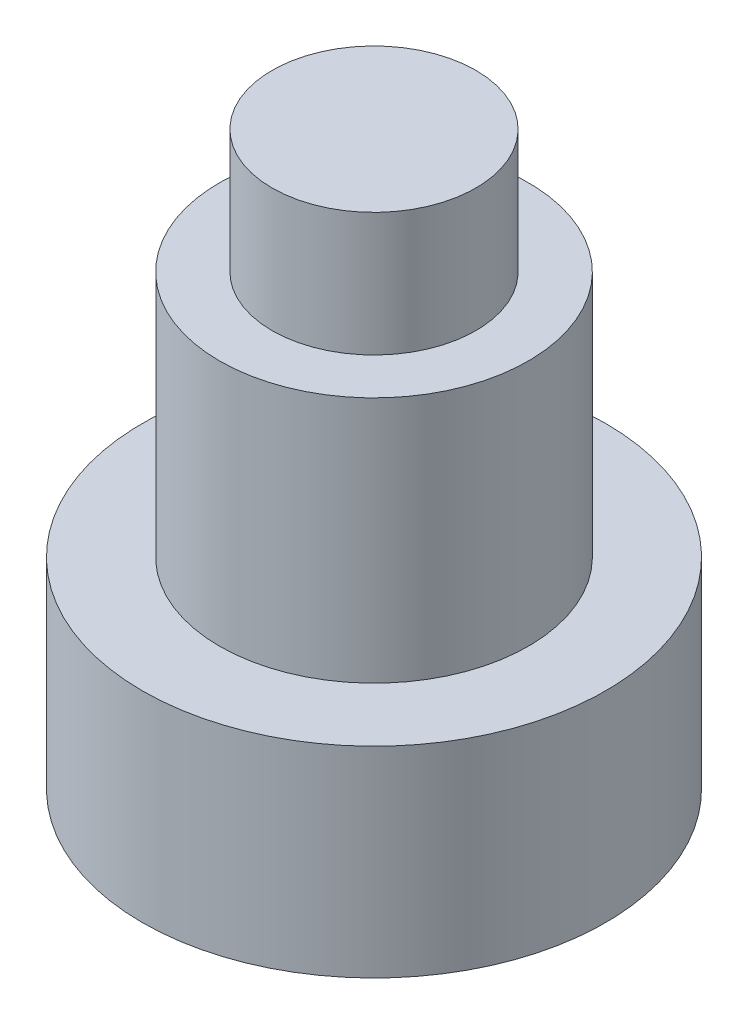
SolidWorks part; units mm, degrees
ref_plane "Front Plane" through (0, 0, 0) normal (0, 0, 1) x (1, 0, 0)
ref_plane "Top Plane" through (0, 0, 0) normal (0, 1, 0) x (1, 0, 0)
ref_plane "Right Plane" through (0, 0, 0) normal (1, 0, 0) x (0, 0, -1)
sketch "Sketch1" plane through (0, 0, 0) normal (0, 1, 0) x (1, 0, 0)
  circle A0 centre (0, 0) radius 3.75
extrude "Boss-Extrude1" add sketch "Sketch1" along normal blind 7.25
sketch "Sketch2" plane through (0, 7.25, 0) normal (0, 1, 0) x (1, 0, 0)
  circle A0 centre (0, 0) radius 2.5
  circle A1 centre (0, 0) radius 3.75
extrude "Cut-Extrude1" cut sketch "Sketch2" against normal blind 4
sketch "Sketch3" plane through (0, 7.25, 0) normal (0, 1, 0) x (1, 0, 0)
  circle A0 centre (0, 0) radius 1.65
extrude "Boss-Extrude2" add sketch "Sketch3" along normal blind 2
